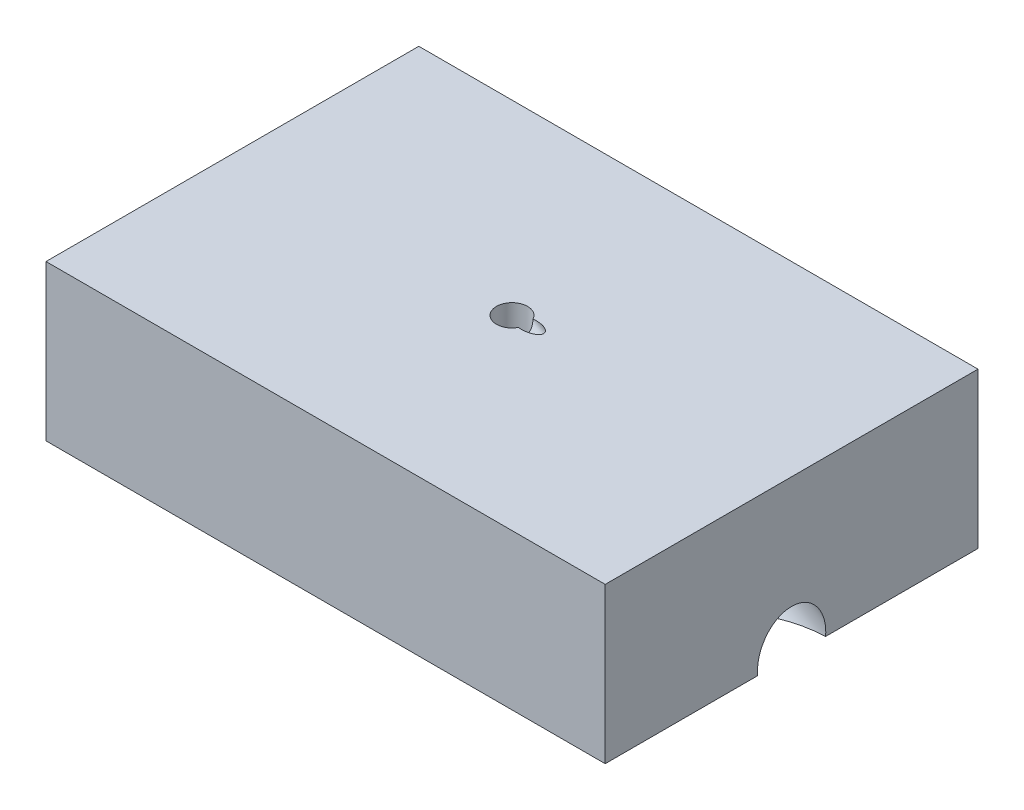
SolidWorks part; units mm, degrees
ref_plane "Front Plane" through (0, 0, 0) normal (0, 0, 1) x (1, 0, 0)
ref_plane "Top Plane" through (0, 0, 0) normal (0, 1, 0) x (1, 0, 0)
ref_plane "Right Plane" through (0, 0, 0) normal (1, 0, 0) x (0, 0, -1)
sketch "Sketch2" plane through (0, 0, 0) normal (0, 1, 0) x (1, 0, 0)
  line L1 (45, -30) -> (-45, -30)
  line L2 (45, -30) -> (45, 30)
  line L3 (45, 30) -> (-45, 30)
  line L4 (-45, -30) -> (-45, 30)
  line L5 (45, -30) -> (-45, 30) construction
  line L6 (45, 30) -> (-45, -30) construction
  point P0 (0, 0)
  dimension "D1" = 90
  dimension "D2" = 60
extrude "Boss-Extrude1" add sketch "Sketch2" along normal blind 25
sketch "Sketch11" plane through (0, 25, 0) normal (0, 1, 0) x (1, 0, 0)
  circle A0 centre (0, 0) radius 2.5
  dimension "D1" = 5
extrude "Cut-Extrude8" cut sketch "Sketch11" against normal blind 5.2
sketch "Sketch17" plane through (0, 19.8, 0) normal (0, 1, 0) x (1, 0, 0)
  circle A0 centre (0, 0) radius 6.25
  dimension "D1" = 12.5
extrude "Cut-Extrude14" cut sketch "Sketch17" against normal blind 2
sketch "Sketch18" plane through (0, 17.8, 0) normal (0, 1, 0) x (1, 0, 0)
  circle A0 centre (0, 0) radius 6.75
  dimension "D1" = 13.5
extrude "Cut-Extrude15" cut sketch "Sketch18" against normal through all
hole_wizard "M4x0.7 Tapped Hole3" [suppressed] positions "Sketch32" profile "Sketch33" tap size "M4x0.7" standard "ANSI Metric"
sketch "Sketch32" plane through (0, 25, 0) normal (0, 1, 0) x (1, 0, 0)
  line L0 (0, 30) -> (0, -30) construction
  line L1 (45, 30) -> (-45, 30) construction
  line L2 (-45, -30) -> (45, -30) construction
  line L11 (0, 26) -> (26, 26) construction
  line L16 (45, 30) -> (-45, 30) construction
  point P50 (0, 26)
  point P64 (26, 26)
  point P84 (-26, 26)
  point P85 (26, -26)
  point P86 (0, -26)
  point P87 (-26, -26)
  dimension "D1" = 2
  dimension "D3" = 4
  dimension "D2" = 26
sketch "Sketch33" plane through (0, 25, -26) normal (1, 0, 0) x (0, 0, 1)
  line L0 (0, 0) -> (0, 11.0914)
  line L1 (0, 11.0914) -> (1.65, 10.1)
  line L2 (1.65, 10.1) -> (1.65, 0)
  line L5 (1.65, 0) -> (0, 0)
  line L10 (0, 11.0914) -> (-1.65, 10.1) construction
  line L11 (0, -6.35) -> (0, 107.95) construction
  dimension "Tap Drill Dia." = 3.3
  dimension "Tap Drill Depth" = 10.1
  dimension "Drill Angle" = 118
cosmetic thread "Hole Thread1" [suppressed] parameters "D1"=8, "D2"=4
cosmetic thread "Hole Thread2" [suppressed] parameters "D1"=8, "D2"=4
cosmetic thread "Hole Thread3" [suppressed] parameters "D1"=8, "D2"=4
cosmetic thread "Hole Thread4" [suppressed] parameters "D1"=8, "D2"=4
cosmetic thread "Hole Thread5" [suppressed] parameters "D1"=8, "D2"=4
cosmetic thread "Hole Thread6" [suppressed] parameters "D1"=8, "D2"=4
sketch3d "3DSketch1" plane through (0, 0, 0) normal (0, 0, 1) x (1, 0, 0)
  dimension "plane" = 300
sketch "Sketch20" plane through (13.8397, -7.9904, 0) normal (-0.866, 0.5, 0) x (0, 0, 1)
  circle A0 centre (0, 23) radius 5.5
  dimension "D1" = 11
  dimension "D2" = 23
extrude "Cut-Extrude17" cut sketch "Sketch20" against normal blind 30 and the other way blind 6.21
sketch "Sketch26" plane through (8.4617, -4.8854, 0) normal (0.866, -0.5, 0) x (0, 0, -1)
  circle A0 centre (0, 23) radius 1.2
  dimension "D1" = 2.4
extrude "Cut-Extrude20" cut sketch "Sketch26" against normal through all contours A0
ref_plane "Plane1" through (0, 0, 0) normal (0, -1, 0) x (-1, 0, 0)
ref_plane "Plane2" through (21.4521, -12.3854, 0) normal (0.866, -0.5, 0) x (0, 0, -1)
hole_wizard "Ø4.0 (4) Diameter Hole1" [suppressed] positions "Sketch37" profile "Sketch36" hole size "Ø4.0" standard "ANSI Metric"
sketch "Sketch37" plane through (0, 25, 0) normal (0, 1, 0) x (1, 0, 0)
  line L4 (0, 30) -> (0, -30) construction
  line L5 (45, 30) -> (-45, 30) construction
  line L6 (-45, -30) -> (45, -30) construction
  point P17 (37.5, 25)
  point P20 (-37.5, 25)
  point P21 (37.5, -25)
  point P22 (-37.5, -25)
  dimension "D1" = 37.5
  dimension "D2" = 5
sketch "Sketch36" plane through (37.5, 25, -25) normal (1, 0, 0) x (0, 0, 1)
  line L0 (0, 0) -> (0, 25)
  line L1 (0, 25) -> (2, 25)
  line L2 (2, 25) -> (2, 0)
  line L5 (2, 0) -> (0, 0)
  line L11 (0, -6.35) -> (0, 107.95) construction
  dimension "Thru Hole Dia." = 4
  dimension "Thru Hole Depth" = 25
sketch "Sketch29" plane through (0, 0, 0) normal (0, -1, 0) x (-1, 0, 0)
  circle A0 centre (0, 0) radius 15
  dimension "D1" = 30
extrude "Cut-Extrude22" [suppressed] cut sketch "Sketch29" against normal blind 10
sketch "Sketch30" plane through (21.4521, -12.3854, 0) normal (0.866, -0.5, 0) x (0, 0, -1)
  circle A0 centre (0, 23) radius 15
  dimension "D1" = 30
extrude "Cut-Extrude23" [suppressed] cut sketch "Sketch30" along normal blind 15
